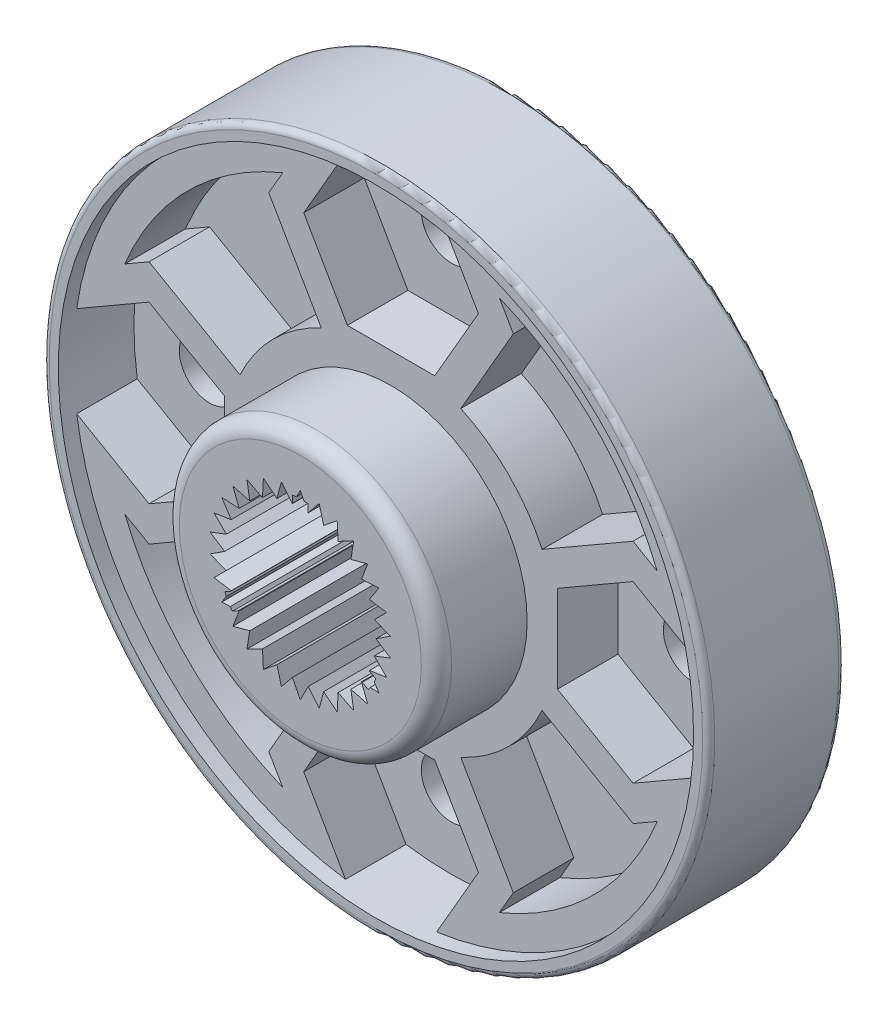
SolidWorks part; units mm, degrees
ref_plane "前视基准面" through (0, 0, 0) normal (0, 0, 1) x (1, 0, 0)
ref_plane "上视基准面" through (0, 0, 0) normal (0, 1, 0) x (1, 0, 0)
ref_plane "右视基准面" through (0, 0, 0) normal (1, 0, 0) x (0, 0, -1)
sketch "草图1" plane through (0, 0, 0) normal (0, 0, 1) x (1, 0, 0)
  circle A0 centre (0, 0) radius 11
  dimension "D1" = 22
extrude "拉伸1" add sketch "草图1" along normal blind 4.5
sketch "草图2" plane through (0, 0, 4.5) normal (0, 0, 1) x (1, 0, 0)
  circle A0 centre (0, 0) radius 4.5
  dimension "D1" = 9
extrude "拉伸2" add sketch "草图2" along normal blind 2.5
sketch "草图3" plane through (0, 0, 0) normal (0, 0, -1) x (-1, 0, 0)
  circle A0 centre (0, 0) radius 3.75
  dimension "D1" = 7.5
extrude "拉伸3" add sketch "草图3" along normal blind 0.5
sketch "草图4" plane through (0, 0, -0.5) normal (0, 0, -1) x (-1, 0, 0)
  circle A0 centre (0, 0) radius 2.75
  dimension "D1" = 5.5
extrude "切除-拉伸1" cut sketch "草图4" against normal blind 2
sketch "草图5" plane through (0, 0, 7) normal (0, 0, 1) x (1, 0, 0)
  line L0 (0, 3) -> (0, -3) construction
  line L1 (0, 3) -> (-0.2613, 2.4863)
  line L2 (-3, 0) -> (3, 0) construction
  line L3 (0, 3) -> (0.2613, 2.4863)
  line L4 (0, 0) -> (-0.2613, 2.4863) construction
  line L5 (0.6237, 2.9344) -> (0.7725, 2.3776)
  line L6 (0.2613, 2.4863) -> (0, 0) construction
  line L7 (0.6237, 2.9344) -> (0.2613, 2.4863)
  line L8 (1.2202, 2.7406) -> (1.25, 2.1651)
  line L9 (1.2202, 2.7406) -> (0.7725, 2.3776)
  line L10 (1.7634, 2.4271) -> (1.6728, 1.8579)
  line L11 (1.7634, 2.4271) -> (1.25, 2.1651)
  line L12 (2.2294, 2.0074) -> (2.0225, 1.4695)
  line L13 (2.2294, 2.0074) -> (1.6728, 1.8579)
  line L14 (2.5981, 1.5) -> (2.2839, 1.0168)
  line L15 (2.5981, 1.5) -> (2.0225, 1.4695)
  line L16 (2.8532, 0.9271) -> (2.4454, 0.5198)
  line L17 (2.8532, 0.9271) -> (2.2839, 1.0168)
  line L18 (2.9836, 0.3136) -> (2.5, 0)
  line L19 (2.9836, 0.3136) -> (2.4454, 0.5198)
  line L20 (2.9836, -0.3136) -> (2.4454, -0.5198)
  line L21 (2.9836, -0.3136) -> (2.5, 0)
  line L22 (2.8532, -0.9271) -> (2.2839, -1.0168)
  line L23 (2.8532, -0.9271) -> (2.4454, -0.5198)
  line L24 (2.5981, -1.5) -> (2.0225, -1.4695)
  line L25 (2.5981, -1.5) -> (2.2839, -1.0168)
  line L26 (2.2294, -2.0074) -> (1.6728, -1.8579)
  line L27 (2.2294, -2.0074) -> (2.0225, -1.4695)
  line L28 (1.7634, -2.4271) -> (1.25, -2.1651)
  line L29 (1.7634, -2.4271) -> (1.6728, -1.8579)
  line L30 (1.2202, -2.7406) -> (0.7725, -2.3776)
  line L31 (1.2202, -2.7406) -> (1.25, -2.1651)
  line L32 (0.6237, -2.9344) -> (0.2613, -2.4863)
  line L33 (0.6237, -2.9344) -> (0.7725, -2.3776)
  line L34 (0, -3) -> (-0.2613, -2.4863)
  line L35 (0, -3) -> (0.2613, -2.4863)
  line L36 (-0.6237, -2.9344) -> (-0.7725, -2.3776)
  line L37 (-0.6237, -2.9344) -> (-0.2613, -2.4863)
  line L38 (-1.2202, -2.7406) -> (-1.25, -2.1651)
  line L39 (-1.2202, -2.7406) -> (-0.7725, -2.3776)
  line L40 (-1.7634, -2.4271) -> (-1.6728, -1.8579)
  line L41 (-1.7634, -2.4271) -> (-1.25, -2.1651)
  line L42 (-2.2294, -2.0074) -> (-2.0225, -1.4695)
  line L43 (-2.2294, -2.0074) -> (-1.6728, -1.8579)
  line L44 (-2.5981, -1.5) -> (-2.2839, -1.0168)
  line L45 (-2.5981, -1.5) -> (-2.0225, -1.4695)
  line L46 (-2.8532, -0.9271) -> (-2.4454, -0.5198)
  line L47 (-2.8532, -0.9271) -> (-2.2839, -1.0168)
  line L48 (-2.9836, -0.3136) -> (-2.5, 0)
  line L49 (-2.9836, -0.3136) -> (-2.4454, -0.5198)
  line L50 (-2.9836, 0.3136) -> (-2.4454, 0.5198)
  line L51 (-2.9836, 0.3136) -> (-2.5, 0)
  line L52 (-2.8532, 0.9271) -> (-2.2839, 1.0168)
  line L53 (-2.8532, 0.9271) -> (-2.4454, 0.5198)
  line L54 (-2.5981, 1.5) -> (-2.0225, 1.4695)
  line L55 (-2.5981, 1.5) -> (-2.2839, 1.0168)
  line L56 (-2.2294, 2.0074) -> (-1.6728, 1.8579)
  line L57 (-2.2294, 2.0074) -> (-2.0225, 1.4695)
  line L58 (-1.7634, 2.4271) -> (-1.25, 2.1651)
  line L59 (-1.7634, 2.4271) -> (-1.6728, 1.8579)
  line L60 (-1.2202, 2.7406) -> (-0.7725, 2.3776)
  line L61 (-1.2202, 2.7406) -> (-1.25, 2.1651)
  line L62 (-0.6237, 2.9344) -> (-0.2613, 2.4863)
  line L63 (-0.6237, 2.9344) -> (-0.7725, 2.3776)
  circle A0 centre (0, 0) radius 3 construction
  circle A1 centre (0, 0) radius 2.5 construction
  dimension "D1" = 6
  dimension "D2" = 5
  dimension "D3" = 12
extrude "切除-拉伸2" cut sketch "草图5" against normal blind 5
sketch "草图6" plane through (0, 0, 0) normal (0, 0, -1) x (-1, 0, 0)
  line L0 (-11, 0) -> (11, 0) construction
  line L2 (0, 11) -> (0, -11) construction
  circle A0 centre (0, 0) radius 11 construction
  circle A1 centre (0, 0) radius 8 construction
  circle A2 centre (0, 8) radius 1
  circle A3 centre (8, 0) radius 1
  circle A4 centre (0, -8) radius 1
  circle A5 centre (-8, 0) radius 1
  dimension "D1" = 16
  dimension "D2" = 2
extrude "切除-拉伸3" cut sketch "草图6" against normal through all
sketch "草图7" plane through (0, 0, 0) normal (0, 0, -1) x (-1, 0, 0)
  line L1 (0, 5.1962) -> (-4.5, -2.5981) construction
  line L2 (-4.5, -2.5981) -> (4.5, -2.5981) construction
  line L3 (4.5, -2.5981) -> (0, 5.1962) construction
  line L4 (0, 5.1962) -> (-4.5, 2.5981) construction
  line L5 (-4.5, 2.5981) -> (-4.5, -2.5981) construction
  line L6 (-4.5, -2.5981) -> (0, -5.1962) construction
  line L7 (0, -5.1962) -> (4.5, -2.5981) construction
  line L8 (4.5, -2.5981) -> (4.5, 2.5981) construction
  line L9 (4.5, 2.5981) -> (0, 5.1962) construction
  circle A0 centre (0, 0) radius 2.5981 construction
  circle A1 centre (0, 0) radius 4.5 construction
  circle A2 centre (0, 5.1962) radius 0.75
  circle A3 centre (4.5, 2.5981) radius 0.75
  circle A4 centre (4.5, -2.5981) radius 0.75
  circle A5 centre (0, -5.1962) radius 0.75
  circle A6 centre (-4.5, -2.5981) radius 0.75
  circle A7 centre (-4.5, 2.5981) radius 0.75
  dimension "D2" = 1.5
  dimension "D1" = 9
extrude "切除-拉伸4" cut sketch "草图7" against normal blind 0.2
sketch "草图8" plane through (0, 0, 0) normal (0, 0, -1) x (-1, 0, 0)
  circle A0 centre (0, 5.1962) radius 1
  circle A1 centre (-4.5, -2.5981) radius 1
  circle A2 centre (4.5, -2.5981) radius 1
  dimension "D1" = 2
extrude "切除-拉伸5" cut sketch "草图8" against normal blind 0.2
sketch "草图9" plane through (0, 0, 0.2) normal (0, 0, -1) x (-1, 0, 0)
  text T0 "1" font "宋体" height 1.5
extrude "拉伸4" add sketch "草图9" along normal blind 0.1
sketch "草图10" plane through (0, 0, 0.2) normal (0, 0, -1) x (-1, 0, 0)
  text T0 "2" font "宋体" height 1.5
extrude "拉伸5" add sketch "草图10" along normal blind 0.1
sketch "草图11" plane through (0, 0, 0.2) normal (0, 0, -1) x (-1, 0, 0)
  text T0 "3" font "宋体" height 1.5
extrude "拉伸6" add sketch "草图11" along normal blind 0.1
sketch "草图12" plane through (0, 0, 4.5) normal (0, 0, 1) x (1, 0, 0)
  circle A0 centre (0, 0) radius 10.5
  circle A1 centre (0, 0) radius 11 construction
  circle A2 centre (0, 0) radius 4.5
  dimension "D1" = 0.5
extrude "切除-拉伸7" cut sketch "草图12" against normal blind 0.5
sketch "草图13" plane through (0, 0, 4) normal (0, 0, 1) x (1, 0, 0)
  line L0 (4.0415, 8) -> (3.5797, 8.7998)
  line L1 (2.8868, 8) -> (1.4434, 10.5)
  line L2 (0, 10.5) -> (-1.4434, 10.5)
  line L3 (-1.4434, 10.5) -> (-2.8868, 8)
  line L4 (-2.8868, 8) -> (-1.4434, 5.5)
  line L5 (-1.4434, 5.5) -> (1.4434, 5.5)
  line L6 (1.4434, 5.5) -> (2.8868, 8)
  line L7 (4.0415, 8) -> (2.0207, 11.5) construction
  line L8 (-3.5797, 8.7998) -> (-4.0415, 8)
  line L9 (-4.0415, 8) -> (-2.0207, 4.5)
  line L10 (-2.0207, 4.5) -> (2.0207, 4.5)
  line L11 (2.0207, 4.5) -> (4.0415, 8)
  line L12 (8, -4.0415) -> (8.7998, -3.5797)
  line L13 (8, -2.8868) -> (10.5, -1.4434)
  line L14 (10.5, -1.4434) -> (10.5, 1.4434)
  line L15 (10.5, 1.4434) -> (8, 2.8868)
  line L16 (8, 2.8868) -> (5.5, 1.4434)
  line L17 (5.5, 1.4434) -> (5.5, -1.4434)
  line L18 (5.5, -1.4434) -> (8, -2.8868)
  line L19 (-2.0207, 11.5) -> (-4.0415, 8) construction
  line L20 (8.7998, 3.5797) -> (8, 4.0415)
  line L21 (8, 4.0415) -> (4.5, 2.0207)
  line L22 (4.5, 2.0207) -> (4.5, -2.0207)
  line L23 (4.5, -2.0207) -> (8, -4.0415)
  line L24 (-4.0415, -8) -> (-3.5797, -8.7998)
  line L25 (-2.8868, -8) -> (-1.4434, -10.5)
  line L26 (-1.4434, -10.5) -> (1.4434, -10.5)
  line L27 (1.4434, -10.5) -> (2.8868, -8)
  line L28 (2.8868, -8) -> (1.4434, -5.5)
  line L29 (1.4434, -5.5) -> (-1.4434, -5.5)
  line L30 (-1.4434, -5.5) -> (-2.8868, -8)
  line L31 (1.4434, 10.5) -> (-1.4434, 10.5) construction
  line L32 (3.5797, -8.7998) -> (4.0415, -8)
  line L33 (4.0415, -8) -> (2.0207, -4.5)
  line L34 (2.0207, -4.5) -> (-2.0207, -4.5)
  line L35 (-2.0207, -4.5) -> (-4.0415, -8)
  line L36 (-8, 4.0415) -> (-8.7998, 3.5797)
  line L37 (-8, 2.8868) -> (-10.5, 1.4434)
  line L38 (-10.5, 1.4434) -> (-10.5, -1.4434)
  line L39 (-10.5, -1.4434) -> (-8, -2.8868)
  line L40 (-8, -2.8868) -> (-5.5, -1.4434)
  line L41 (-5.5, -1.4434) -> (-5.5, 1.4434)
  line L42 (-5.5, 1.4434) -> (-8, 2.8868)
  line L43 (2.8868, 8) -> (1.4434, 10.5) construction
  line L44 (-8.7998, -3.5797) -> (-8, -4.0415)
  line L45 (-8, -4.0415) -> (-4.9934, -2.3056)
  line L46 (0, 10.5) -> (1.4434, 10.5)
  line L47 (-4.9934, 2.3056) -> (-8, 4.0415)
  line L101 (2.0207, 11.5) -> (-2.0207, 11.5) construction
  line L105 (-4.5, -2.0207) -> (-4.5, 2.0207) [skipped]
  arc A0 (-2.3056, 4.9934) -> (-4.9934, 2.3056) centre (0, 0) ccw
  arc A1 (-3.5797, 8.7998) -> (-8.7998, 3.5797) centre (0, 0) ccw
  circle A3 centre (0, 8) radius 2.5 construction
  circle A4 centre (8, 0) radius 2.5 construction
  circle A5 centre (0, -8) radius 2.5 construction
  circle A6 centre (-8, 0) radius 2.5 construction
  arc A8 (-8.7998, -3.5797) -> (-3.5797, -8.7998) centre (0, 0) ccw
  arc A9 (4.9934, 2.3056) -> (2.3056, 4.9934) centre (0, 0) ccw
  arc A10 (2.3056, -4.9934) -> (4.9934, -2.3056) centre (0, 0) ccw
  arc A11 (-4.9934, -2.3056) -> (-2.3056, -4.9934) centre (0, 0) ccw
  arc A13 (8.7998, 3.5797) -> (3.5797, 8.7998) centre (0, 0) ccw
  arc A14 (3.5797, -8.7998) -> (8.7998, -3.5797) centre (0, 0) ccw
  circle M1 centre (-8, 0) radius 1
  circle M2 centre (8, 0) radius 1
  circle M4 centre (0, 0) radius 10.5
  circle M5 centre (0, -8) radius 1
  circle M6 centre (0, 8) radius 1
  dimension "D1" = 19
  dimension "D2" = 11
  dimension "D4" = 1
  dimension "D3" = 5
extrude "切除-拉伸9" cut sketch "草图13" against normal blind 2 contours L5 L6 L1 L3 L4 M4 M6 | L17 L18 L13 L15 L16 M4 M2 | L29 L30 L25 L27 L28 M4 M5 | L41 L42 L37 L39 L40 M4 M1 | L8 A1 L36 L47 A0 L9 | L20 A13 L0 L11 A9 L21 | L32 A14 L12 L23 A10 L33 | A11 L45 L44 A8 L24 L35
fillet "圆角1" radius 0.5 1 edges at (4.5, 0, 7)
sketch "草图14" plane through (0, 0, 1.5) normal (0, 0, -1) x (-1, 0, 0)
  line L0 (0, 2.75) -> (0, -2.75) construction
  line L1 (-0.25, 2.7386) -> (-0.25, 1.479)
  line L2 (-2.75, 0) -> (2.75, 0) construction
  line L3 (0.25, 2.7386) -> (0.25, 1.479)
  line L4 (2.4967, -1.1528) -> (1.4059, -0.523)
  line L5 (2.2467, -1.5858) -> (1.1559, -0.956)
  line L6 (-2.2467, -1.5858) -> (-1.1559, -0.956)
  line L7 (-2.4967, -1.1528) -> (-1.4059, -0.523)
  circle A0 centre (0, 0) radius 2.75 construction
  circle A1 centre (0, 0) radius 2.75 construction
  arc A2 (-0.25, 1.479) -> (-1.4059, -0.523) centre (0, 0) ccw
  arc A3 (0.25, 2.7386) -> (-0.25, 2.7386) centre (0, 0) ccw
  arc A4 (-2.4967, -1.1528) -> (-2.2467, -1.5858) centre (0, 0) ccw
  arc A5 (2.2467, -1.5858) -> (2.4967, -1.1528) centre (0, 0) ccw
  arc A6 (-1.1559, -0.956) -> (1.1559, -0.956) centre (0, 0) ccw
  arc A7 (1.4059, -0.523) -> (0.25, 1.479) centre (0, 0) ccw
  dimension "D1" = 3
  dimension "D2" = 0.5
extrude "切除-拉伸10" cut sketch "草图14" against normal through all
fillet "圆角2" radius 0.2 2 edges at (11, 0, 4.5) (11, 0, 0)
